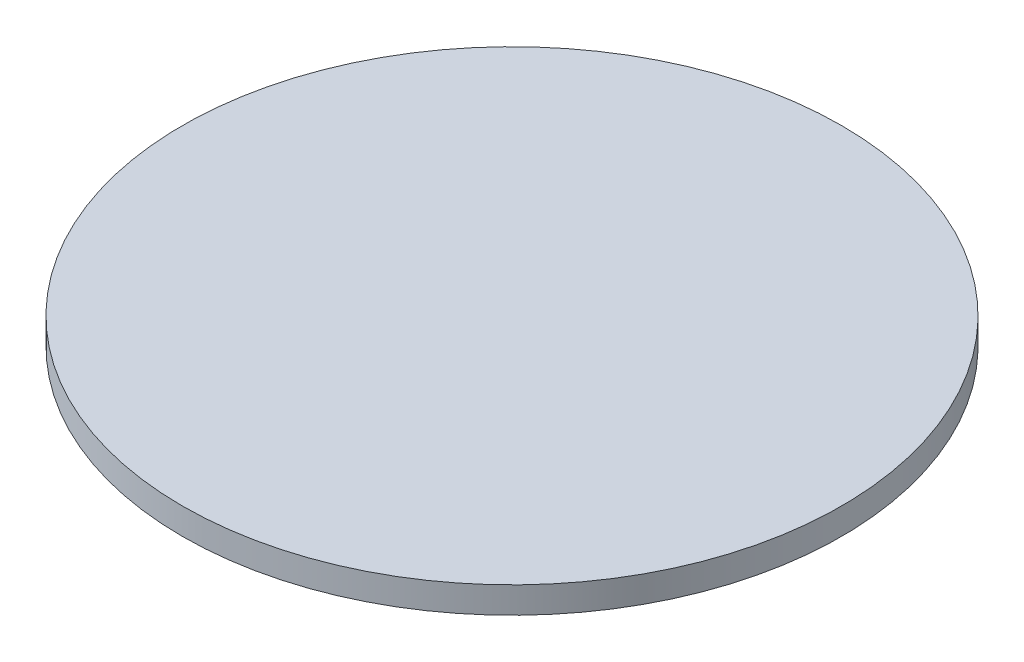
SolidWorks part; units mm, degrees
material "Glass"
ref_plane "Front Plane" through (0, 0, 0) normal (0, 0, 1) x (1, 0, 0)
ref_plane "Top Plane" through (0, 0, 0) normal (0, 1, 0) x (1, 0, 0)
ref_plane "Right Plane" through (0, 0, 0) normal (1, 0, 0) x (0, 0, -1)
sketch "Sketch1" plane through (0, 0, 0) normal (0, 1, 0) x (1, 0, 0)
  circle A0 centre (0, 0) radius 25
  dimension "D1" = 50
extrude "Boss-Extrude1" add sketch "Sketch1" along normal blind 2
